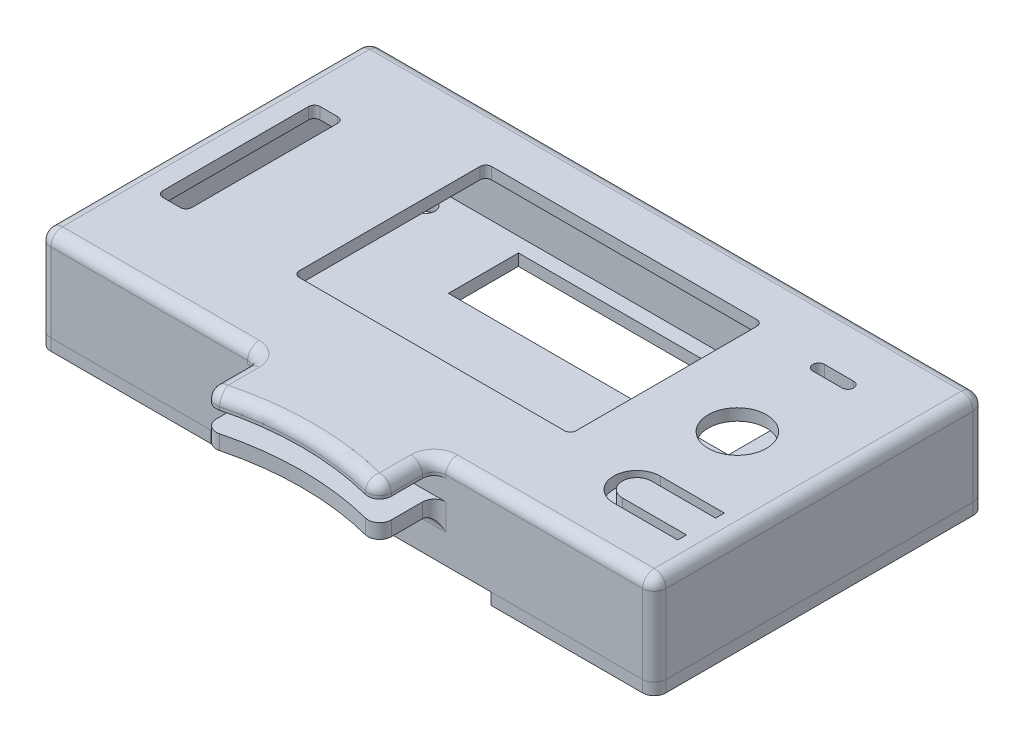
SolidWorks part; units mm, degrees
ref_plane "Alzado" through (0, 0, 0) normal (0, 0, 1) x (1, 0, 0)
ref_plane "Planta" through (0, 0, 0) normal (0, 1, 0) x (1, 0, 0)
ref_plane "Vista lateral" through (0, 0, 0) normal (1, 0, 0) x (0, 0, -1)
sketch "Croquis1" plane through (0, 0, 0) normal (0, 1, 0) x (1, 0, 0)
  line L0 (-2.25, 54.45) -> (103.25, 54.45)
  line L1 (0, 0) -> (101, 0) construction
  line L2 (0, 0) -> (0, 52.2) construction
  line L3 (0, 52.2) -> (101, 52.2) construction
  line L4 (101, 0) -> (101, 52.2) construction
  line L5 (26.6, 45.5) -> (74.1, 45.5)
  line L6 (26.6, 45.5) -> (26.6, 12.5)
  line L7 (26.6, 12.5) -> (74.1, 12.5)
  line L8 (74.1, 45.5) -> (74.1, 12.5)
  line L9 (3, 39.7) -> (8, 39.7)
  line L10 (3, 39.7) -> (3, 12.7)
  line L11 (3, 12.7) -> (8, 12.7)
  line L12 (8, 39.7) -> (8, 12.7)
  line L13 (103.25, -2.25) -> (103.25, 54.45)
  line L14 (-2.25, -2.25) -> (103.25, -2.25)
  line L15 (-2.25, -2.25) -> (-2.25, 54.45)
  line L16 (88.05, 12.48) -> (99.05, 12.48)
  line L17 (88.05, 7.48) -> (99.05, 7.48)
  line L18 (88.05, 5.98) -> (99.05, 5.98)
  line L19 (88.05, 13.98) -> (99.05, 13.98)
  line L20 (99.05, 13.98) -> (99.05, 12.48)
  line L21 (99.05, 7.48) -> (99.05, 5.98)
  line L22 (90.55, 43.65) -> (85.55, 43.65) construction
  line L23 (90.55, 42.65) -> (85.55, 42.65)
  line L24 (90.55, 44.65) -> (85.55, 44.65)
  line L25 (-0.75, -0.75) -> (101.75, -0.75) construction
  line L26 (101.75, -0.75) -> (101.75, 52.95) construction
  line L27 (-0.75, 52.95) -> (101.75, 52.95) construction
  line L28 (-0.75, -0.75) -> (-0.75, 52.95) construction
  circle A0 centre (98.3, 49.5) radius 1.6 construction
  circle A1 centre (98.3, 2.7) radius 1.6 construction
  circle A2 centre (12.3, 49.5) radius 1.6 construction
  circle A3 centre (12.3, 2.7) radius 1.6 construction
  circle A4 centre (88.05, 27.2) radius 5
  circle A5 centre (88.05, 43.65) radius 3 construction
  arc A6 (88.05, 12.48) -> (88.05, 7.48) centre (88.05, 9.98) ccw
  arc A7 (88.05, 13.98) -> (88.05, 5.98) centre (88.05, 9.98) ccw
  arc A8 (90.55, 42.65) -> (90.55, 44.65) centre (90.55, 43.65) ccw
  arc A9 (85.55, 44.65) -> (85.55, 42.65) centre (85.55, 43.65) ccw
  point P41 (88.05, 43.65)
  point P50 (0, 0)
  dimension "D3" = 3.2
  dimension "D6" = 2.7
  dimension "D12" = 10
  dimension "D15" = 6
  dimension "D17" = 5
  dimension "D1" = 52.2
  dimension "D2" = 101
  dimension "D4" = 46.8
  dimension "D5" = 2.7
  dimension "D7" = 86
  dimension "D8" = 47.5
  dimension "D9" = 33
  dimension "D10" = 12.5
  dimension "D11" = 26.9
  dimension "D13" = 12.95
  dimension "D14" = 25
  dimension "D16" = 8.55
  dimension "D18" = 17.22
  dimension "D19" = 27
  dimension "D20" = 5
  dimension "D21" = 12.5
  dimension "D22" = 8
  dimension "D24" = 11
  dimension "D25" = 1.5
  dimension "D26" = 5
  dimension "D27" = 2
  dimension "D23" = 1.5
  dimension "D28" = 0.75
extrude "Saliente-Extruir1" add sketch "Croquis1" along normal blind 2
sketch "Croquis5" plane through (0, 0, 0) normal (0, -1, 0) x (1, 0, 0)
  line L8 (-2.25, 2.25) -> (-2.25, -54.45) construction
  line L9 (-2.25, 2.25) -> (103.25, 2.25) construction
  line L10 (103.25, 2.25) -> (103.25, -54.45) construction
  line L11 (-2.25, -54.45) -> (103.25, -54.45) construction
  line L12 (-2.25, 2.25) -> (-2.25, -54.45)
  line L13 (-2.25, 2.25) -> (103.25, 2.25)
  line L14 (103.25, 2.25) -> (103.25, -54.45)
  line L15 (-2.25, -54.45) -> (103.25, -54.45)
  line L16 (101.75, 0.75) -> (101.75, -52.95) construction
  line L17 (-0.75, 0.75) -> (101.75, 0.75) construction
  line L18 (-0.75, 0.75) -> (-0.75, -52.95) construction
  line L19 (-0.75, -52.95) -> (101.75, -52.95) construction
  line L20 (101.75, 0.75) -> (101.75, -52.95)
  line L21 (-0.75, 0.75) -> (101.75, 0.75)
  line L22 (-0.75, 0.75) -> (-0.75, -52.95)
  line L23 (-0.75, -52.95) -> (101.75, -52.95)
extrude "Saliente-Extruir4" add sketch "Croquis5" along normal blind 13.5
sketch "Croquis6" plane through (0, -13.5, 0) normal (0, -1, 0) x (1, 0, 0)
  line L0 (103.25, 2.25) -> (103.25, -54.45) construction
  line L1 (-2.25, 2.25) -> (103.25, 2.25) construction
  line L2 (-2.25, 2.25) -> (-2.25, -54.45) construction
  line L3 (-2.25, -54.45) -> (103.25, -54.45) construction
  line L4 (103.25, 2.25) -> (103.25, -54.45)
  line L5 (-2.25, 2.25) -> (27.25, 2.25)
  line L6 (-2.25, 2.25) -> (-2.25, -54.45)
  line L7 (-2.25, -54.45) -> (103.25, -54.45)
  line L8 (50.5, 2.25) -> (50.5, -54.45) construction
  line L9 (-0.75, 0.75) -> (-0.75, -52.95) construction
  line L14 (9.45, -48.95) -> (2.45, -48.95)
  line L15 (9.45, -48.95) -> (9.45, -3.95)
  line L16 (9.45, -3.95) -> (2.45, -3.95)
  line L17 (2.45, -48.95) -> (2.45, -3.95)
  line L18 (-0.75, -52.95) -> (101.75, -52.95) construction
  line L19 (103.25, -26.1) -> (-2.25, -26.1) construction
  line L20 (75.25, -50.45) -> (27.25, -50.45)
  line L21 (75.25, -50.45) -> (75.25, -38.45)
  line L22 (75.25, -38.45) -> (27.25, -38.45)
  line L23 (27.25, -50.45) -> (27.25, -38.45)
  line L25 (75.25, 2.25) -> (75.25, -3.75)
  line L26 (75.25, -3.75) -> (27.25, -3.75)
  line L27 (27.25, 2.25) -> (27.25, -3.75)
  line L28 (75.25, 2.25) -> (103.25, 2.25)
  circle A0 centre (98.3, -2.7) radius 1.6 construction
  circle A1 centre (12.3, -49.5) radius 1.6 construction
  circle A2 centre (12.3, -49.5) radius 1.6
  circle A3 centre (98.3, -49.5) radius 1.6 construction
  circle A4 centre (98.3, -2.7) radius 1.6
  circle A7 centre (98.3, -49.5) radius 1.6
  circle A14 centre (12.3, -2.7) radius 1.6 construction
  circle A15 centre (12.3, -2.7) radius 1.6
  circle A16 centre (80.5, -26.1) radius 1.55
  circle A17 centre (20.5, -26.1) radius 1.55
  dimension "D5" = 48
  dimension "D11" = 3.1
  dimension "D1" = 45
  dimension "D2" = 7
  dimension "D3" = 3.2
  dimension "D4" = 4
  dimension "D6" = 12
  dimension "D7" = 2.5
  dimension "D8" = 28
  dimension "D9" = 48
  dimension "D10" = 6
  dimension "D12" = 30
extrude "Saliente-Extruir5" add sketch "Croquis6" along normal blind 2
ref_plane "Plano1" through (0, -13.5, 0) normal (0, -1, 0) x (-1, 0, 0)
sketch "Croquis8" plane through (0, 0, 0) normal (0, -1, 0) x (1, 0, 0)
  line L0 (0, 0) -> (101, 0) construction
  line L2 (9.225, 0.75) -> (9.225, -6.25)
  line L3 (9.225, -6.25) -> (15.375, -6.25)
  line L4 (15.375, 0.75) -> (15.375, -6.25)
  line L5 (101, -26.1) -> (-2.25, -26.1) construction
  line L6 (101, 0) -> (101, -52.2) construction
  line L7 (-2.25, 2.25) -> (-2.25, -54.45) construction
  line L8 (50.5, 0) -> (50.5, -52.2) construction
  line L9 (0, -52.2) -> (101, -52.2) construction
  line L17 (101.75, -6.25) -> (95.6, -6.25)
  line L18 (95.6, 0.75) -> (95.6, -6.25)
  line L23 (101.75, 0.75) -> (101.75, -52.95) construction
  line L24 (-0.75, 0.75) -> (101.75, 0.75) construction
  line L25 (95.6, 0.75) -> (101.75, 0.75)
  line L26 (101.75, 0.75) -> (101.75, -6.25)
  line L27 (9.225, 0.75) -> (15.375, 0.75)
  line L28 (9.225, -52.95) -> (15.375, -52.95)
  line L29 (15.375, -52.95) -> (15.375, -45.95)
  line L30 (9.225, -45.95) -> (15.375, -45.95)
  line L31 (9.225, -52.95) -> (9.225, -45.95)
  line L32 (101.75, -52.95) -> (101.75, -45.95)
  line L33 (95.6, -52.95) -> (101.75, -52.95)
  line L34 (101.75, -45.95) -> (95.6, -45.95)
  line L35 (95.6, -52.95) -> (95.6, -45.95)
  dimension "D1" = 6.15
  dimension "D2" = 7
  dimension "D3" = 3.075
  dimension "D4" = 7
  dimension "D5" = 6.15
extrude "Saliente-Extruir13" add sketch "Croquis8" along normal blind 9
sketch "Croquis9" plane through (0, -9, 0) normal (0, -1, 0) x (1, 0, 0)
  circle A0 centre (12.3, -2.7) radius 2.15
  circle A1 centre (98.3, -2.7) radius 2.15
  circle A2 centre (98.3, -49.5) radius 2.15
  circle A3 centre (12.3, -49.5) radius 2.15
  dimension "D1" = 4.3
extrude "Cortar-Extruir2" cut sketch "Croquis9" against normal blind 3.5
split "Partir1" trim tools "Plano1" bodies to split 108 resulting bodies 111 112
fillet "Redondeo6" radius 1 8 edges at (8, 1, -39.7) (3, 1, -39.7) (3, 1, -12.7) (8, 1, -12.7) (26.6, 1, -12.5) (74.1, 1, -12.5) (74.1, 1, -45.5) (26.6, 1, -45.5)
fillet "Redondeo7" radius 1 18 edges at (101.75, -4.5, -6.25) (100.4, 0, -6.25) (95.6, 0, -2.615) (95.6, -4.5, 0.75) (9.225, -4.5, 0.75) (9.225, 0, -2.75) (12.3, 0, -6.25) (15.375, 0, -2.75) (15.375, -4.5, 0.75) (9.225, -4.5, -52.95) (9.225, 0, -49.45) (12.3, 0, -45.95) (15.375, 0, -49.45) (15.375, -4.5, -52.95) (95.6, -4.5, -52.95) (101.75, -4.5, -45.95) (98.675, 0, -45.95) (95.6, 0, -49.45)
sketch "Croquis10" plane through (0, 0, 0) normal (0, -1, 0) x (1, 0, 0)
  circle A0 centre (88.05, -9.98) radius 2.5
extrude "Saliente-Extruir14" add sketch "Croquis10" along normal blind 2 contours A0
sketch "Croquis13" plane through (0, 0, 2.25) normal (0, 0, 1) x (1, 0, 0)
  line L0 (50.5, 2) -> (50.5, -13.5) construction
  line L1 (-2.25, 2) -> (103.25, 2) construction
  line L2 (103.25, -13.5) -> (-2.25, -13.5) construction
  line L4 (35.5, 2) -> (65.5, 2)
  line L5 (35.5, 2) -> (35.5, -0.5)
  line L6 (35.5, -0.5) -> (65.5, -0.5)
  line L7 (65.5, 2) -> (65.5, -0.5)
  line L8 (35.5, -4) -> (65.5, -4)
  line L9 (35.5, -4) -> (35.5, -6.5)
  line L10 (35.5, -6.5) -> (65.5, -6.5)
  line L11 (65.5, -4) -> (65.5, -6.5)
  dimension "D1" = 30
  dimension "D2" = 2.5
  dimension "D3" = 15
  dimension "D4" = 2.5
  dimension "D5" = 30
  dimension "D6" = 15
  dimension "D7" = 3.5
extrude "Saliente-Extruir16" add sketch "Croquis13" along normal blind 10
sketch "Croquis14" plane through (0, 2, 0) normal (0, 1, 0) x (1, 0, 0)
  line L0 (65.5, -12.25) -> (35.5, -12.25) construction
  line L1 (65.5, -12.25) -> (35.5, -12.25)
  arc A0 (35.5, -12.25) -> (65.5, -12.25) centre (50.5, -59.947) cw
  dimension "D1" = 50
extrude "Cortar-Extruir3" cut sketch "Croquis14" against normal up to surface (8.5 mm away) up to face at (50.5, -6.5, 7.25)
fillet "Redondeo8" radius 2 21 edges at (84.375, 2, 2.25) (35.5, 0.75, 2.25) (35.5, 2, 7.25) (65.5, 0.75, 2.25) (65.5, 2, 7.25) (35.5, 0.75, 12.25) (65.5, 0.75, 12.25) (35.5, -5.25, 2.25) (50.5, -6.5, 2.25) (65.5, -5.25, 2.25) (35.5, -5.25, 12.25) (65.5, -5.25, 12.25) (50.5, 2, 9.947) (-2.25, 2, -26.1) (16.625, 2, 2.25) (103.25, 2, -26.1) (50.5, 2, -54.45) (-2.25, -5.75, -54.45) (103.25, -5.75, -54.45) (103.25, -5.75, 2.25) (-2.25, -5.75, 2.25)
fillet "Redondeo9" radius 2 4 edges at (103.25, -14.5, -54.45) (-2.25, -14.5, -54.45) (103.25, -14.5, 2.25) (-2.25, -14.5, 2.25)
